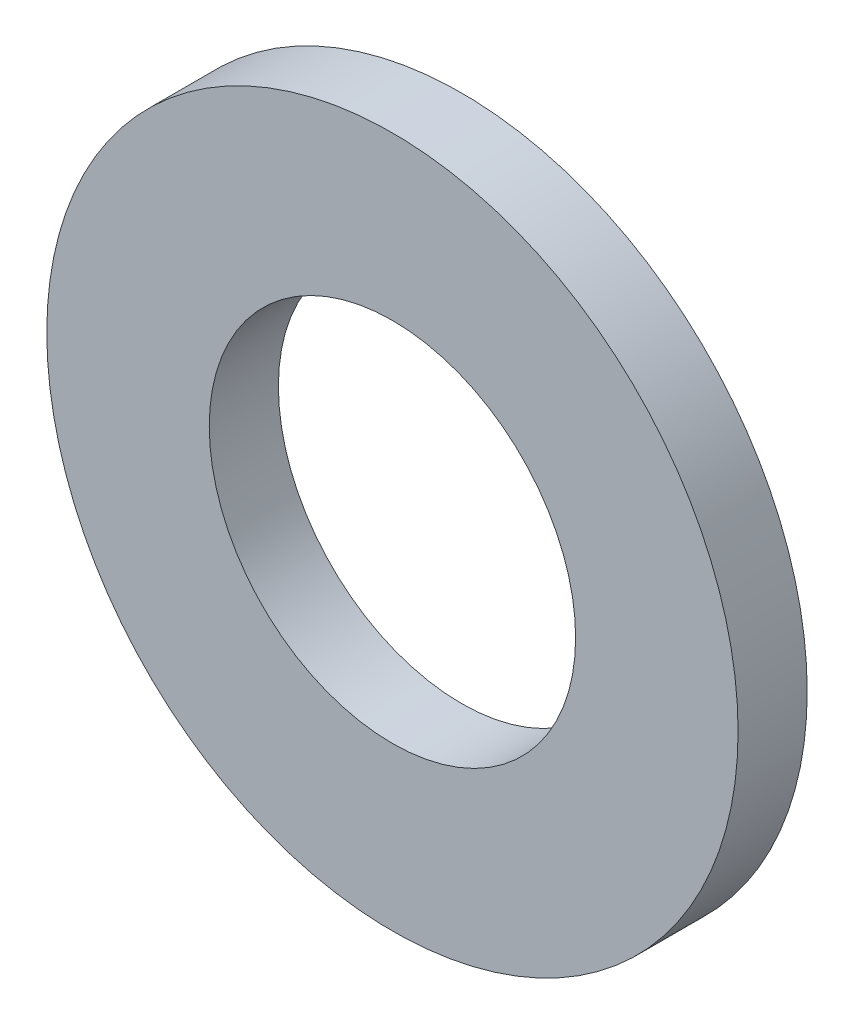
SolidWorks part; units mm, degrees
ref_plane "Front" through (0, 0, 0) normal (0, 0, 1) x (1, 0, 0)
ref_plane "Top" through (0, 0, 0) normal (0, 1, 0) x (1, 0, 0)
ref_plane "Right" through (0, 0, 0) normal (1, 0, 0) x (0, 0, -1)
sketch "Sketch1" plane through (0, 0, 0) normal (0, 0, 1) x (1, 0, 0)
  circle A0 centre (0, 0) radius 2.65
  circle A1 centre (0, 0) radius 5
  dimension "d1" = 5.3
  dimension "d2" = 10
extrude "Base-Extrude" add sketch "Sketch1" against normal blind 1
